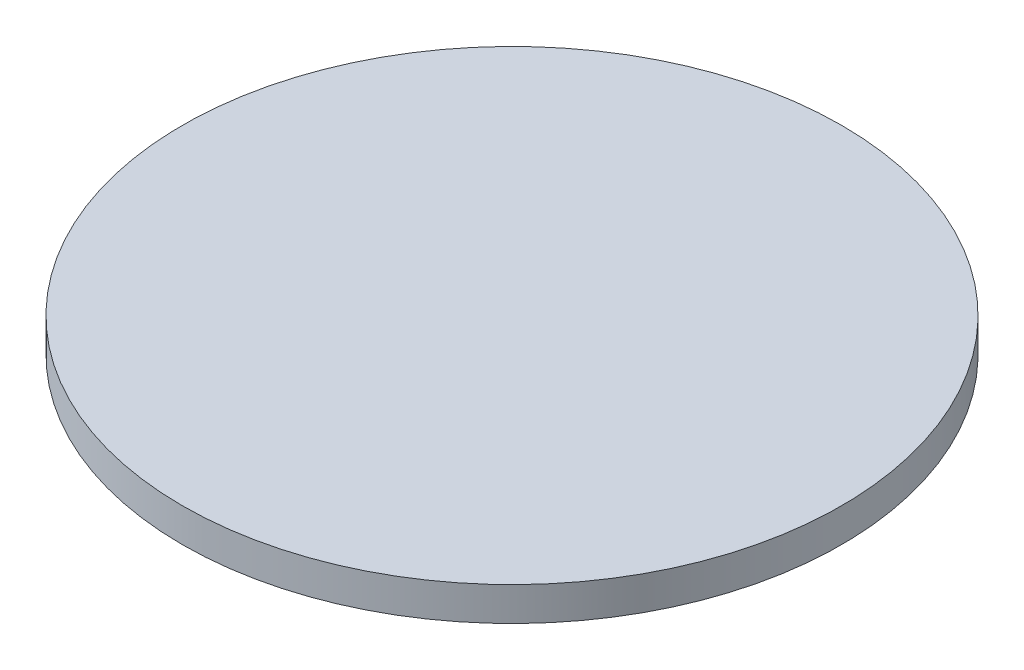
SolidWorks part; units mm, degrees
ref_plane "Plan de face" through (0, 0, 0) normal (0, 0, 1) x (1, 0, 0)
ref_plane "Plan de dessus" through (0, 0, 0) normal (0, 1, 0) x (1, 0, 0)
ref_plane "Plan de droite" through (0, 0, 0) normal (1, 0, 0) x (0, 0, -1)
sketch "Esquisse1" plane through (0, 0, 0) normal (0, 1, 0) x (1, 0, 0)
  circle A0 centre (0, 0) radius 21.5
  dimension "D1" = 43
extrude "Boss.-Extru.1" add sketch "Esquisse1" along normal blind 2.2
